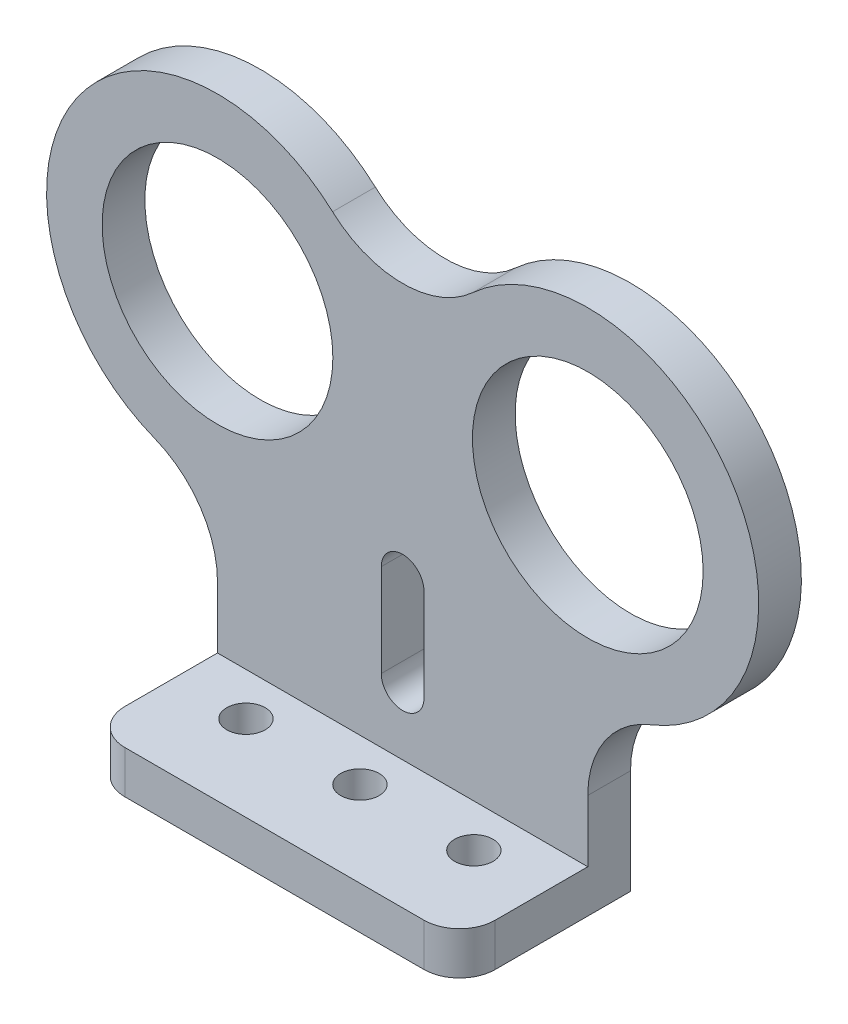
SolidWorks part; units mm, degrees
material "PA Type 6"
ref_plane "Front Plane" through (0, 0, 0) normal (0, 0, 1) x (1, 0, 0)
ref_plane "Top Plane" through (0, 0, 0) normal (0, 1, 0) x (1, 0, 0)
ref_plane "Right Plane" through (0, 0, 0) normal (1, 0, 0) x (0, 0, -1)
sketch "Sketch1" plane through (0, 0, 0) normal (0, 0, 1) x (1, 0, 0)
  line L0 (-25, 0) -> (25, 0)
  line L1 (25, 0) -> (25, 25)
  line L2 (0, 0) -> (0, 50) construction
  line L3 (25, 25) -> (-25, 25) construction
  line L4 (-25, 0) -> (-25, 25)
  line L5 (-13, 7.3365) -> (-13, 0)
  line L6 (13, 7.3365) -> (13, 0)
  line L7 (0, 14) -> (0, 7.5) construction
  line L8 (1.5, 14) -> (1.5, 7.5)
  line L9 (-1.5, 14) -> (-1.5, 7.5)
  circle A0 centre (13, 25) radius 8.1
  arc A1 (25, 25) -> (4.9185, 33.8707) centre (13, 25) ccw
  arc A2 (-25, 25) -> (-4.9185, 33.8707) centre (-13, 25) cw
  circle A3 centre (-13, 25) radius 8.1
  arc A4 (-4.9185, 33.8707) -> (4.9185, 33.8707) centre (0, 39.2697) ccw
  arc A5 (-25, 25) -> (-17.4211, 13.8441) centre (-13, 25) ccw
  arc A6 (-17.4211, 13.8441) -> (-13, 7.3365) centre (-20, 7.3365) cw
  arc A7 (25, 25) -> (17.4211, 13.8441) centre (13, 25) cw
  arc A8 (17.4211, 13.8441) -> (13, 7.3365) centre (20, 7.3365) ccw
  arc A9 (1.5, 14) -> (-1.5, 14) centre (0, 14) ccw
  arc A10 (-1.5, 7.5) -> (1.5, 7.5) centre (0, 7.5) ccw
  point P10 (0, 25)
  point P25 (0, 10.75)
  dimension "D2" = 16.2
  dimension "D5" = 7
  dimension "D1" = 25
  dimension "D3" = 13
  dimension "D4" = 25
  dimension "D6" = 6.5
  dimension "D7" = 7.5
  dimension "D8" = 3
extrude "Boss-Extrude1" add sketch "Sketch1" along normal blind 3 contours A8 A7 A1 A4 A2 A5 A6 L5 L0 L6 A0 A3
sketch "Sketch3" plane through (0, 0, 0) normal (0, -1, 0) x (1, 0, 0)
  line L0 (0, 12) -> (0, 0) construction
  line L1 (-13, 3) -> (13, 3)
  line L2 (-13, 3) -> (-13, 9.5)
  line L3 (-10.5, 12) -> (10.5, 12)
  line L4 (13, 3) -> (13, 9.5)
  line L5 (0, 6) -> (8, 6) construction
  circle A0 centre (8, 6) radius 1.35
  circle A1 centre (-8, 6) radius 1.35
  arc A2 (-13, 9.5) -> (-10.5, 12) centre (-10.5, 9.5) cw
  arc A3 (10.5, 12) -> (13, 9.5) centre (10.5, 9.5) cw
  circle A4 centre (0, 6) radius 1.35
  point P18 (13, 12)
  dimension "D3" = 2.7
  dimension "D4" = 2.5
  dimension "D5" = 2.7
  dimension "D1" = 9
  dimension "D2" = 8
extrude "Boss-Extrude2" add sketch "Sketch3" against normal blind 3
